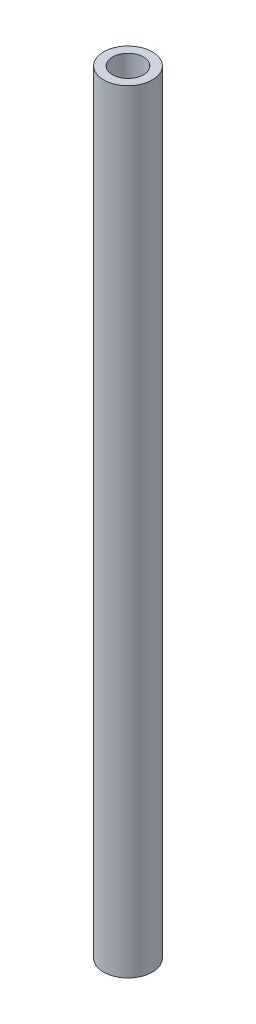
SolidWorks part; units mm, degrees
ref_plane "前视基准面" through (0, 0, 0) normal (0, 0, 1) x (1, 0, 0)
ref_plane "上视基准面" through (0, 0, 0) normal (0, 1, 0) x (1, 0, 0)
ref_plane "右视基准面" through (0, 0, 0) normal (1, 0, 0) x (0, 0, -1)
sketch "草图1" plane through (0, 0, 0) normal (0, 1, 0) x (1, 0, 0)
  circle A0 centre (0, 0) radius 2
  circle A1 centre (0, 0) radius 3.15
  dimension "D1" = 4
  dimension "D2" = 6.3
extrude "凸台-拉伸1" add sketch "草图1" along normal blind 100
